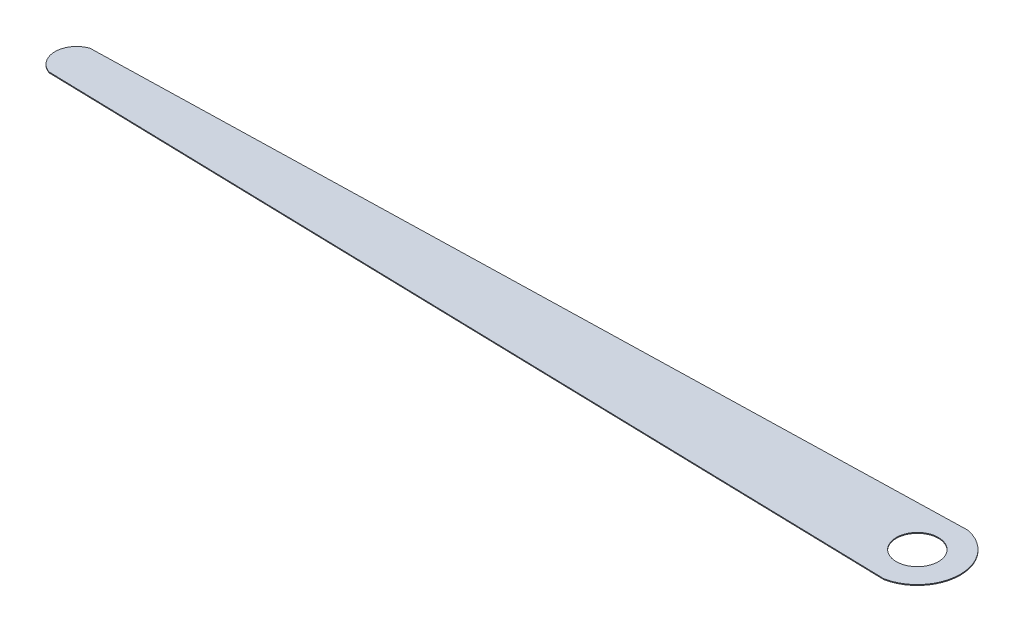
SolidWorks part; units mm, degrees
ref_plane "Front Plane" through (0, 0, 0) normal (0, 0, 1) x (1, 0, 0)
ref_plane "Top Plane" through (0, 0, 0) normal (0, 1, 0) x (1, 0, 0)
ref_plane "Right Plane" through (0, 0, 0) normal (1, 0, 0) x (0, 0, -1)
sketch "Sketch1" plane through (0, 0, 0) normal (0, 1, 0) x (1, 0, 0)
  line L0 (0, 0) -> (-101.8735, -2.5644)
  line L1 (-101.8735, -7.4356) -> (0, -10)
  arc A0 (-101.8735, -2.5644) -> (-101.8735, -7.4356) centre (-101.0288, -5) ccw
  arc A1 (0, 0) -> (0, -10) centre (-1.0288, -5) cw
  circle A2 centre (-1.0288, -5) radius 2.5
  dimension "D1" = 100
  dimension "D3" = 5.1047
  dimension "D4" = 2.5779
  dimension "D6" = 5
  dimension "D2" = 10
  dimension "D5" = 101.8735
extrude "Boss-Extrude1" add sketch "Sketch1" along normal blind 0.1
